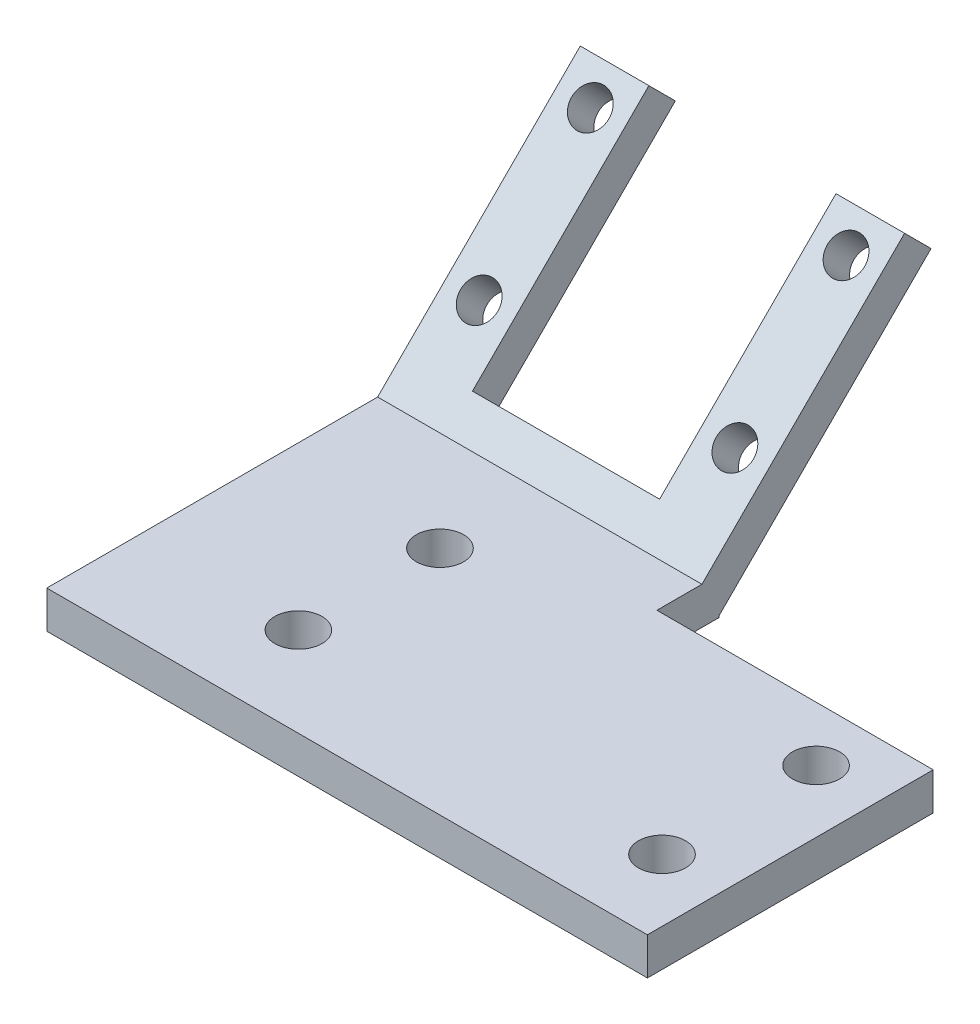
SolidWorks part; units mm, degrees
ref_plane "Front Plane" through (0, 0, 0) normal (0, 0, 1) x (1, 0, 0)
ref_plane "Top Plane" through (0, 0, 0) normal (0, 1, 0) x (1, 0, 0)
ref_plane "Right Plane" through (0, 0, 0) normal (1, 0, 0) x (0, 0, -1)
sketch "Sketch2" plane through (0, 0, 0) normal (0, 1, 0) x (1, 0, 0)
  line L1 (-28.075, 11.175) -> (20.075, 11.175)
  line L2 (-28.075, 11.175) -> (-28.075, -15.3459)
  line L3 (-28.075, -15.3459) -> (20.075, -15.3459)
  line L4 (20.075, 11.175) -> (20.075, -15.3459)
  circle A0 centre (-15.075, -8.175) radius 1.89
  circle A1 centre (-15.075, 3.175) radius 1.89
  circle A2 centre (15.075, 3.175) radius 1.89
  circle A3 centre (15.075, -9.175) radius 1.89
extrude "Boss-Extrude1" add sketch "Sketch2" along normal blind 3
ref_plane "Plane3" through (0, -4.0875, -4.0875) normal (0, -0.7071, -0.7071) x (-1, 0, 0)
sketch "Sketch6" plane through (0, -4.0875, -4.0875) normal (0, -0.7071, -0.7071) x (-1, 0, 0)
  line L0 (28.075, 10.0232) -> (28.075, 7.9019) construction
  line L1 (28.075, 8.9626) -> (2.075, 8.9626)
  line L2 (28.075, 8.9626) -> (28.075, 33)
  line L3 (28.075, 33) -> (2.075, 33)
  line L4 (2.075, 8.9626) -> (2.075, 33)
  line L6 (7.575, 33.0051) -> (22.575, 33.0051)
  line L7 (7.575, 33.0051) -> (7.575, 13)
  line L8 (7.575, 13) -> (22.575, 13)
  line L9 (22.575, 33.0051) -> (22.575, 13)
  circle A0 centre (4.825, 30.25) radius 1.5
  circle A1 centre (25.325, 30.25) radius 1.5
  circle A2 centre (4.825, 17.65) radius 1.5
  circle A3 centre (25.325, 17.65) radius 1.5
  dimension "D1" = 2.75
  dimension "D2" = 2.75
  dimension "D3" = 2.75
  dimension "D4" = 2.75
  dimension "D5" = 2.75
  dimension "D6" = 12.6
  dimension "D7" = 2.75
  dimension "D8" = 12.6
  dimension "D9" = 5.5
  dimension "D10" = 5.5
  dimension "D11" = 20
extrude "Boss-Extrude2" add sketch "Sketch6" along normal blind 3 contours L3 L9 L8 L7 L4 L1 L2 A3 A2 A1 A0
sketch "Sketch7" plane through (0, 0, 0) normal (0, -1, 0) x (1, 0, 0)
  line L0 (-28.075, -11.175) -> (-28.075, 15.3459) construction
  line L1 (-28.075, -10.1692) -> (-2.075, -10.1692)
  line L2 (-28.075, -10.1692) -> (-28.075, -12.5463)
  line L3 (-28.075, -12.5463) -> (-2.075, -12.5463)
  line L4 (-2.075, -10.1692) -> (-2.075, -12.5463)
extrude "Boss-Extrude3" add sketch "Sketch7" against normal blind 2
sketch "Sketch8" plane through (0, 3, 0) normal (0, 1, 0) x (1, 0, 0)
  line L0 (20.075, -15.3459) -> (20.075, 11.175) construction
  line L1 (-2.075, 11.175) -> (20.075, 11.175)
  line L2 (-2.075, 11.175) -> (-2.075, 7.5658)
  line L3 (-2.075, 7.5658) -> (20.075, 7.5658)
  line L4 (20.075, 11.175) -> (20.075, 7.5658)
extrude "Cut-Extrude1" cut sketch "Sketch8" against normal blind 3
